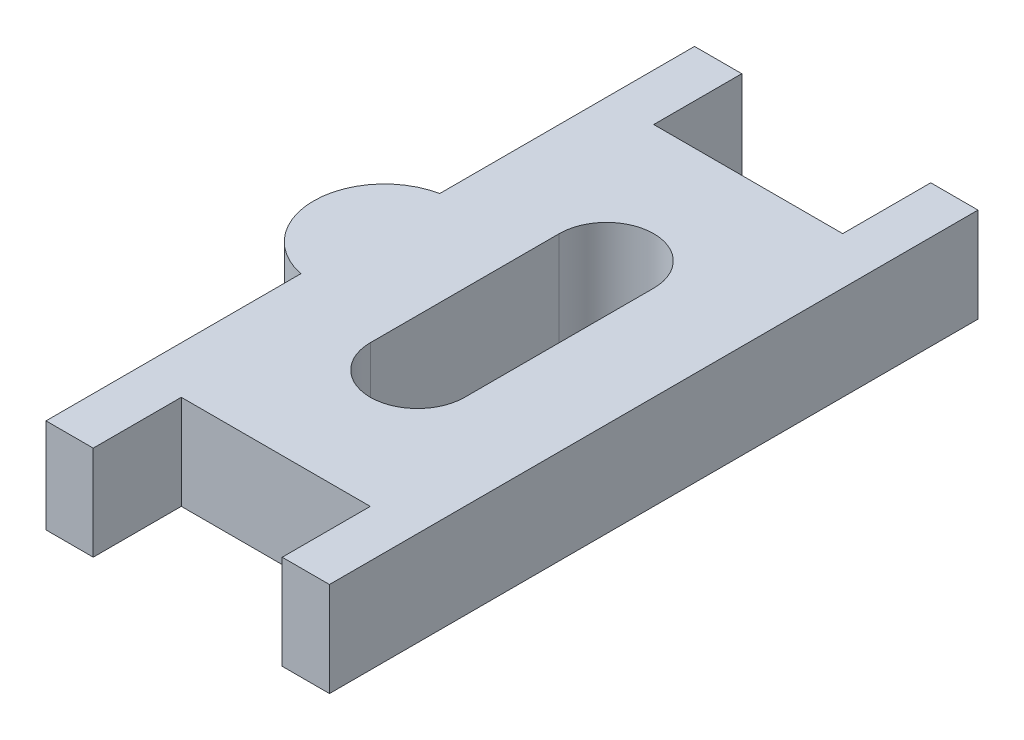
SolidWorks part; units mm, degrees
ref_plane "Front Plane" through (0, 0, 0) normal (0, 0, 1) x (1, 0, 0)
ref_plane "Top Plane" through (0, 0, 0) normal (0, 1, 0) x (1, 0, 0)
ref_plane "Right Plane" through (0, 0, 0) normal (1, 0, 0) x (0, 0, -1)
sketch "Sketch1" plane through (0, 0, 0) normal (0, 1, 0) x (1, 0, 0)
  line L0 (0, -7.9375) -> (0, 7.9375) construction
  line L1 (-4.7625, 10.8966) -> (4.7625, 10.8966)
  line L2 (-4.7625, 10.8966) -> (-4.7625, 7.9375)
  line L3 (-4.7625, 7.9375) -> (4.7625, 7.9375)
  line L4 (4.7625, 10.8966) -> (4.7625, 7.9375)
  line L5 (-4.7625, 10.8966) -> (4.7625, 7.9375) construction
  line L6 (-4.7625, 7.9375) -> (4.7625, 10.8966) construction
  line L7 (-4.7625, -10.8966) -> (4.7625, -10.8966)
  line L8 (-4.7625, -10.8966) -> (-4.7625, -7.9375)
  line L9 (-4.7625, -7.9375) -> (4.7625, -7.9375)
  line L10 (4.7625, -10.8966) -> (4.7625, -7.9375)
  line L11 (-4.7625, -10.8966) -> (4.7625, -7.9375) construction
  line L12 (-4.7625, -7.9375) -> (4.7625, -10.8966) construction
  point P0 (0, 9.417)
  point P5 (0, -9.4171)
  dimension "D1" = 9.525
  dimension "D2" = 2.9591
  dimension "D3" = 15.875
sketch "Sketch2" plane through (0, 0, 0) normal (0, 1, 0) x (1, 0, 0)
  line L0 (-3.175, 10.8966) -> (-3.175, 7.9375)
  line L1 (-4.7625, 10.8966) -> (4.7625, 10.8966) construction
  line L2 (-4.7625, 7.9375) -> (4.7625, 7.9375) construction
  line L3 (-3.175, 7.9375) -> (3.175, 7.9375)
  line L4 (-3.175, 10.8966) -> (-4.7625, 10.8966)
  line L5 (-4.7625, 10.8966) -> (-4.7625, 2.3331)
  line L6 (-4.7625, -10.8966) -> (-4.7625, -7.9375) construction
  line L8 (0, 0) -> (-7.9375, 0) construction
  line L9 (0, 4.0105) -> (0, -3.3928) construction
  line L10 (0, -7.9375) -> (0, 7.9375) construction
  line L11 (4.7625, 10.8966) -> (4.7625, -10.8966)
  line L12 (3.175, 10.8966) -> (4.7625, 10.8966)
  line L13 (3.175, 10.8966) -> (3.175, 7.9375)
  line L14 (0, -4.0105) -> (0, 3.3928) construction
  line L15 (3.175, -10.8966) -> (3.175, -7.9375)
  line L16 (3.175, -10.8966) -> (4.7625, -10.8966)
  line L19 (-4.7625, -10.8966) -> (-4.7625, -2.3331)
  line L20 (-3.175, -10.8966) -> (-4.7625, -10.8966)
  line L21 (-3.175, -7.9375) -> (3.175, -7.9375)
  line L22 (-3.175, -10.8966) -> (-3.175, -7.9375)
  arc A0 (-4.7625, 2.3331) -> (-4.7625, -2.3331) centre (-4.2863, 0) ccw
  point P27 (0, 7.9375)
  point P38 (0, -7.9375)
  dimension "D1" = 2.3813
  dimension "D2" = 1.905
  dimension "D3" = 1.5875
extrude "Boss-Extrude1" add sketch "Sketch2" along normal blind 3.175
sketch "Sketch3" plane through (0, 3.175, 0) normal (0, 1, 0) x (1, 0, 0)
  line L0 (0, 3.175) -> (0, -3.175) construction
  line L1 (1.5875, 3.175) -> (1.5875, -3.175)
  line L2 (-1.5875, 3.175) -> (-1.5875, -3.175)
  arc A0 (1.5875, 3.175) -> (-1.5875, 3.175) centre (0, 3.175) ccw
  arc A1 (-1.5875, -3.175) -> (1.5875, -3.175) centre (0, -3.175) ccw
  point P3 (0, 0)
  dimension "D1" = 1.5875
  dimension "D2" = 6.35
extrude "Cut-Extrude1" cut sketch "Sketch3" against normal up to next
